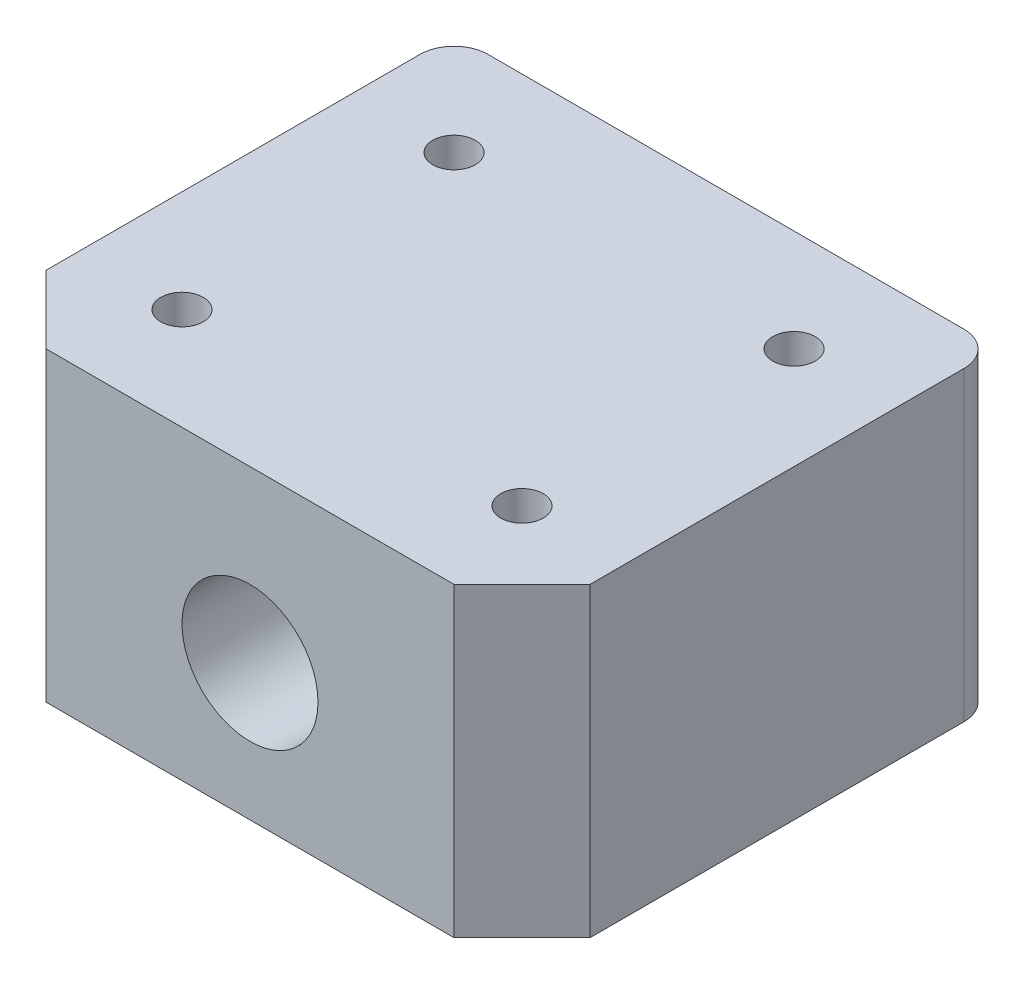
SolidWorks part; units mm, degrees
material "ABS"
ref_plane "Plan de face" through (0, 0, 0) normal (0, 0, 1) x (1, 0, 0)
ref_plane "Plan de dessus" through (0, 0, 0) normal (0, 1, 0) x (1, 0, 0)
ref_plane "Plan de droite" through (0, 0, 0) normal (1, 0, 0) x (0, 0, -1)
sketch "Esquisse1" plane through (0, 0, 0) normal (0, 0, 1) x (1, 0, 0)
  line L1 (-8, 5) -> (8, 5)
  line L2 (-8, 5) -> (-8, -4)
  line L3 (-8, -4) -> (8, -4)
  line L4 (8, 5) -> (8, -4)
  circle A0 centre (0, 0) radius 2
  dimension "D3" = 4
  dimension "D4" = 4
  dimension "D1" = 16
  dimension "D2" = 9
  dimension "D5" = 8
extrude "Boss.-Extru.1" add sketch "Esquisse1" along normal blind 7
sketch "Esquisse2" plane through (0, 5, 0) normal (0, 1, 0) x (1, 0, 0)
  line L0 (-5, -4) -> (5, -4)
  line L1 (8, -7) -> (-8, -7) construction
  line L2 (-8, -7) -> (-8, 0) construction
  dimension "D1" = 3
  dimension "D2" = 3
  dimension "D3" = 10
hole_wizard "Trou taraudé M1.61" positions "Esquisse3D1" profile "Esquisse3" tap size "M1.6" standard "ISO" end condition through all
sketch3d "Esquisse3D1"
  point P2 (-5, 5, 4)
  point P8 (5, 5, 4)
sketch "Esquisse3" plane through (-5, 5, 4) normal (1, 0, 0) x (0, 0, 1)
  line L0 (0, 0) -> (0, 9)
  line L1 (0, 9) -> (0.625, 9)
  line L2 (0.625, 9) -> (0.625, 0)
  line L5 (0.625, 0) -> (0, 0)
  line L11 (0, -6.35) -> (0, 107.95) construction
  dimension "Diamètre principal du filetage" = 1.25
  dimension "Profondeur du trou pour taraudage jusqu'au prochain" = 9
mirror "Symétrie1" about plane through (-8, -4, 0) normal (0, 0, 1) of "Boss.-Extru.1", "Trou taraudé M1.61"
chamfer "Chanfrein1" distance 2 angle 45 2 edges at (-8, 0.5, 7) (8, 0.5, 7)
fillet "Congé1" radius 1 2 edges at (-8, 0.5, -7) (8, 0.5, -7)
equation "\"D5@Esquisse1\" = \"D1@Esquisse1\"/2"
